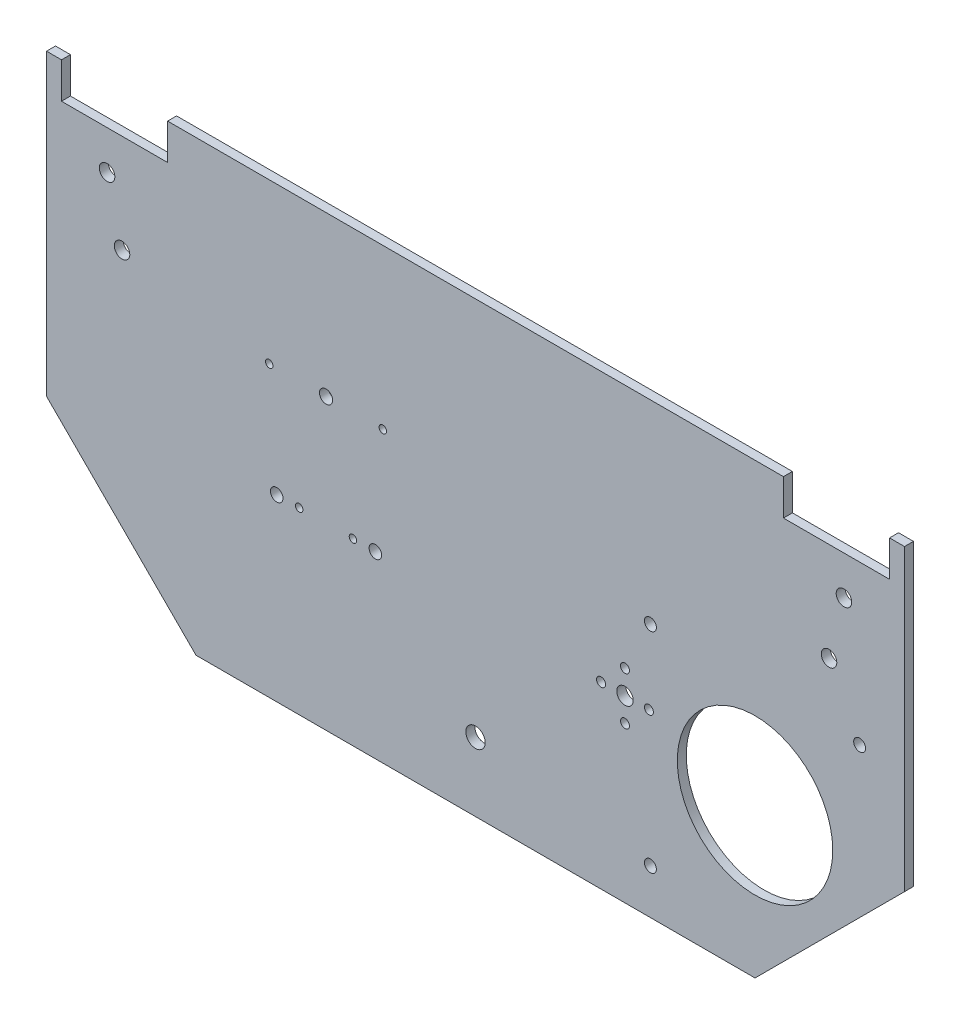
SolidWorks part; units mm, degrees
ref_plane "Front Plane" through (0, 0, 0) normal (0, 0, 1) x (1, 0, 0)
ref_plane "Top Plane" through (0, 0, 0) normal (0, 1, 0) x (1, 0, 0)
ref_plane "Right Plane" through (0, 0, 0) normal (1, 0, 0) x (0, 0, -1)
sketch "Model" plane through (0, 0, 0) normal (0, 0, 1) x (1, 0, 0)
  line L0 (5, 150) -> (0, 150)
  line L1 (5, 138) -> (5, 150)
  line L2 (40.5, 138) -> (5, 138)
  line L3 (40.5, 150) -> (40.5, 138)
  line L4 (246.5, 150) -> (40.5, 150)
  line L5 (246.5, 138) -> (246.5, 150)
  line L6 (282, 138) -> (246.5, 138)
  line L7 (282, 150) -> (282, 138)
  line L8 (287, 150) -> (282, 150)
  line L9 (287, 50) -> (287, 150)
  line L10 (237, 0) -> (287, 50)
  line L11 (50, 0) -> (237, 0)
  line L12 (0, 50) -> (50, 0)
  line L13 (0, 150) -> (0, 50)
  line L14 (193.5, 60) -> (201.5, 60) construction
  line L15 (193.5, 60) -> (193.5, 52) construction
  circle A0 centre (266.75, 125) radius 2.6
  circle A1 centre (261.75, 105) radius 2.6
  circle A2 centre (25.25, 105) radius 2.6
  circle A3 centre (20.25, 125) radius 2.6
  circle A4 centre (74.5, 96.7) radius 1.25
  circle A5 centre (93.5, 96.7) radius 2.2
  circle A6 centre (110, 60) radius 2.1
  circle A7 centre (77, 60) radius 2.1
  circle A8 centre (84.5, 60) radius 1.25
  circle A9 centre (102.5, 60) radius 1.25
  circle A10 centre (112.5, 96.7) radius 1.25
  circle A11 centre (193.5, 60) radius 2.75
  circle A12 centre (201.5, 60) radius 1.5
  circle A13 centre (185.5, 60) radius 1.5
  circle A14 centre (143.5, 23) radius 3.25
  circle A15 centre (193.5, 68) radius 1.5
  circle A16 centre (193.5, 52) radius 1.5
  circle A17 centre (237, 50) radius 26
  point P44 (237, 50)
  dimension "D4" = 52
  dimension "D2" = 90
  dimension "D3" = 8
  dimension "D1" = 2
extrude "Boss-Extrude1" add sketch "Model" along normal blind 3
sketch "Sketch1" plane through (0, 0, 0) normal (0, 0, -1) x (-1, 0, 0)
  circle A0 centre (-202, 85) radius 2 construction
  circle A1 centre (-202, 15) radius 2 construction
  circle A2 centre (-272, 85) radius 2 construction
  circle A3 centre (-202, 85) radius 2
  circle A4 centre (-202, 15) radius 2
  circle A5 centre (-272, 85) radius 2
extrude "Cut-Extrude1" cut sketch "Sketch1" against normal through all
